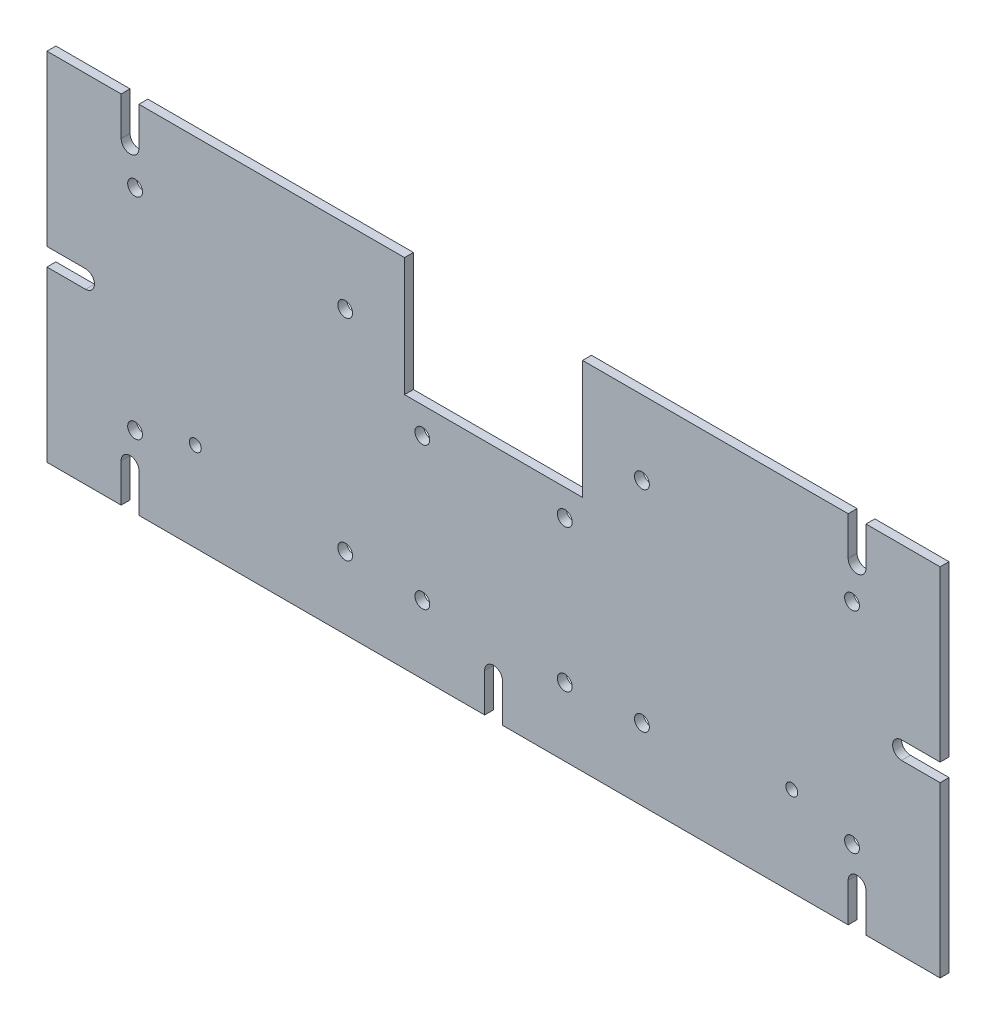
SolidWorks part; units mm, degrees
ref_plane "Front Plane" through (0, 0, 0) normal (0, 0, 1) x (1, 0, 0)
ref_plane "Top Plane" through (0, 0, 0) normal (0, 1, 0) x (1, 0, 0)
ref_plane "Right Plane" through (0, 0, 0) normal (1, 0, 0) x (0, 0, -1)
sketch "Sketch1" plane through (0, 0, 0) normal (0, 0, 1) x (1, 0, 0)
  line L1 (-150.5, -60) -> (150.5, -60)
  line L2 (-150.5, -60) -> (-150.5, 60)
  line L3 (-150.5, 60) -> (150.5, 60)
  line L4 (150.5, -60) -> (150.5, 60)
  line L5 (-150.5, -60) -> (150.5, 60) construction
  line L6 (-150.5, 60) -> (150.5, -60) construction
  point P0 (0, 0)
  dimension "D1" = 301
  dimension "D2" = 120
extrude "Boss-Extrude1" add sketch "Sketch1" along normal blind 3
sketch "Sketch2" plane through (0, 0, 3) normal (0, 0, 1) x (1, 0, 0)
  line L0 (-30, 60) -> (-30, 20)
  line L1 (150.5, 60) -> (-150.5, 60) construction
  line L2 (-30, 20) -> (30, 20)
  line L3 (0, 0) -> (0, 23.4463) construction
  line L4 (30, 60) -> (30, 20)
  line L5 (-30, 60) -> (30, 60)
  line L6 (-150.5, -60) -> (150.5, -60) construction
  point P9 (0, 20)
  point P12 (0, -60)
  dimension "D1" = 30
  dimension "D2" = 40
extrude "Cut-Extrude1" cut sketch "Sketch2" against normal blind 3 contours L5 L4 L2 L0
sketch "Sketch4" plane through (0, 0, 3) normal (0, 0, 1) x (1, 0, 0)
  line L0 (0, 0) -> (0, 20) construction
  line L1 (-30, 20) -> (30, 20) construction
  line L2 (0, 20) -> (0, -60) construction
  line L3 (-150.5, -60) -> (150.5, -60) construction
  line L4 (0, -60) -> (0, 60) construction
  line L5 (-150.5, 0) -> (150.5, 0) construction
  line L6 (150.5, -60) -> (150.5, 60) construction
  line L7 (-125.5, -60) -> (-125.5, -47)
  line L8 (-119.5, -47) -> (-119.5, -60)
  line L9 (-119.5, -60) -> (-125.5, -60)
  line L10 (-150.5, 60) -> (-150.5, -60) construction
  line L11 (3, -47) -> (3, -60)
  line L12 (-3, -60) -> (-3, -47)
  line L13 (3, -60) -> (-3, -60)
  line L14 (125.5, -47) -> (125.5, -60)
  line L15 (119.5, -60) -> (119.5, -47)
  line L16 (125.5, -60) -> (119.5, -60)
  line L17 (0, -20) -> (0, 60) construction
  line L18 (125.5, 60) -> (119.5, 60)
  line L19 (119.5, 60) -> (119.5, 47)
  line L20 (125.5, 47) -> (125.5, 60)
  line L21 (3, 60) -> (-3, 60)
  line L22 (-3, 60) -> (-3, 47)
  line L23 (3, 47) -> (3, 60)
  line L24 (-119.5, 60) -> (-125.5, 60)
  line L25 (-119.5, 47) -> (-119.5, 60)
  line L26 (-125.5, 60) -> (-125.5, 47)
  line L27 (150.5, 3) -> (137.5, 3)
  line L28 (137.5, -3) -> (150.5, -3)
  line L29 (150.5, -3) -> (150.5, 3)
  line L30 (150.5, 3) -> (150.5, -3)
  line L31 (137.5, 3) -> (150.5, 3)
  line L32 (150.5, -3) -> (137.5, -3)
  line L33 (-150.5, -3) -> (-137.5, -3)
  line L34 (-137.5, 3) -> (-150.5, 3)
  line L35 (-150.5, 3) -> (-150.5, -3)
  line L36 (-150.5, -3) -> (-150.5, 3)
  line L37 (-137.5, -3) -> (-150.5, -3)
  line L38 (-150.5, 3) -> (-137.5, 3)
  arc A0 (-125.5, -47) -> (-119.5, -47) centre (-122.5, -47) cw
  arc A1 (-3, -47) -> (3, -47) centre (0, -47) cw
  arc A2 (119.5, -47) -> (125.5, -47) centre (122.5, -47) cw
  arc A3 (119.5, 47) -> (125.5, 47) centre (122.5, 47) ccw
  arc A4 (-3, 47) -> (3, 47) centre (0, 47) ccw
  arc A5 (-125.5, 47) -> (-119.5, 47) centre (-122.5, 47) ccw
  arc A6 (137.5, 3) -> (137.5, -3) centre (137.5, 0) ccw
  arc A7 (-137.5, 3) -> (-137.5, -3) centre (-137.5, 0) cw
  line M21 (-150.5, 60) -> (-150.5, -60)
  line M22 (-150.5, -60) -> (150.5, -60)
  line M23 (150.5, -60) -> (150.5, 60)
  line M24 (150.5, 60) -> (30, 60)
  dimension "D1" = 3
  dimension "D2" = 13
  dimension "D3" = 25
  dimension "D5" = 6
  dimension "D6" = 13
  dimension "D4" = 3
extrude "Cut-Extrude2" cut sketch "Sketch4" against normal blind 10 contours A0 L7 L8 M22 | A7 L34 L33 M21 | A2 L15 L14 M22 | L27 A6 L28 M23 | L19 A3 L20 M24 | L25 L24 L26 A5 | L11 L13 L12 A1
sketch "Sketch5" plane through (0, 0, 3) normal (0, 0, 1) x (1, 0, 0)
  line L0 (30, 60) -> (30, 20) construction
  line L1 (120.8, -35.8) -> (50, -35.8) construction
  line L2 (120.8, -35.8) -> (120.8, 35) construction
  line L3 (120.8, 35) -> (50, 35) construction
  line L4 (50, -35.8) -> (50, 35) construction
  line L5 (120.8, -35.8) -> (50, 35) construction
  line L6 (120.8, 35) -> (50, -35.8) construction
  line L7 (119.5, 60) -> (30, 60) construction
  circle A0 centre (120.8, 35) radius 2.5
  circle A1 centre (120.8, -35.8) radius 2.5
  circle A2 centre (50, 35) radius 2.5
  circle A3 centre (50, -35.8) radius 2.5
  point P0 (85.4, -0.4)
  dimension "D3" = 5
  dimension "D4" = 5
  dimension "D5" = 5
  dimension "D6" = 5
  dimension "D1" = 70.8
  dimension "D2" = 70.8
  dimension "D7" = 20
  dimension "D8" = 25
extrude "Cut-Extrude3" cut sketch "Sketch5" against normal blind 10 contours A0 | A1 | A3 | A2
ref_plane "Plane1" through (0, 0, 0) normal (-1, 0, 0) x (0, 0, 1)
mirror "Mirror1" about plane through (0, 0, 0) normal (-1, 0, 0) of "Cut-Extrude3"
sketch "Sketch6" plane through (0, 0, 3) normal (0, 0, 1) x (1, 0, 0)
  line L0 (-30, 20) -> (30, 20) construction
  line L1 (-24, -37) -> (24, -37) construction
  line L2 (-24, -37) -> (-24, 11) construction
  line L3 (-24, 11) -> (24, 11) construction
  line L4 (24, -37) -> (24, 11) construction
  line L5 (-24, -37) -> (24, 11) construction
  line L6 (-24, 11) -> (24, -37) construction
  circle A0 centre (24, 11) radius 2.5
  circle A1 centre (-24, 11) radius 2.5
  circle A2 centre (-24, -37) radius 2.5
  circle A3 centre (24, -37) radius 2.5
  point P0 (0, -13)
  dimension "D4" = 5
  dimension "D5" = 5
  dimension "D6" = 5
  dimension "D7" = 5
  dimension "D1" = 48
  dimension "D2" = 48
  dimension "D3" = 33
extrude "Cut-Extrude4" cut sketch "Sketch6" against normal blind 10
sketch "Sketch7" plane through (0, 0, 3) normal (0, 0, 1) x (1, 0, 0)
  line L0 (0, 0) -> (0, -44) construction
  line L1 (-119.5, -60) -> (-3, -60) construction
  line L2 (-150.5, -3) -> (-150.5, -60) construction
  arc A0 (3, -47) -> (-3, -47) centre (0, -47) ccw construction
  circle A1 centre (-100.5, -30) radius 2
  circle A2 centre (100.5, -30) radius 2
  dimension "D1" = 4
  dimension "D2" = 30
  dimension "D3" = 50
extrude "Cut-Extrude5" cut sketch "Sketch7" against normal blind 10
